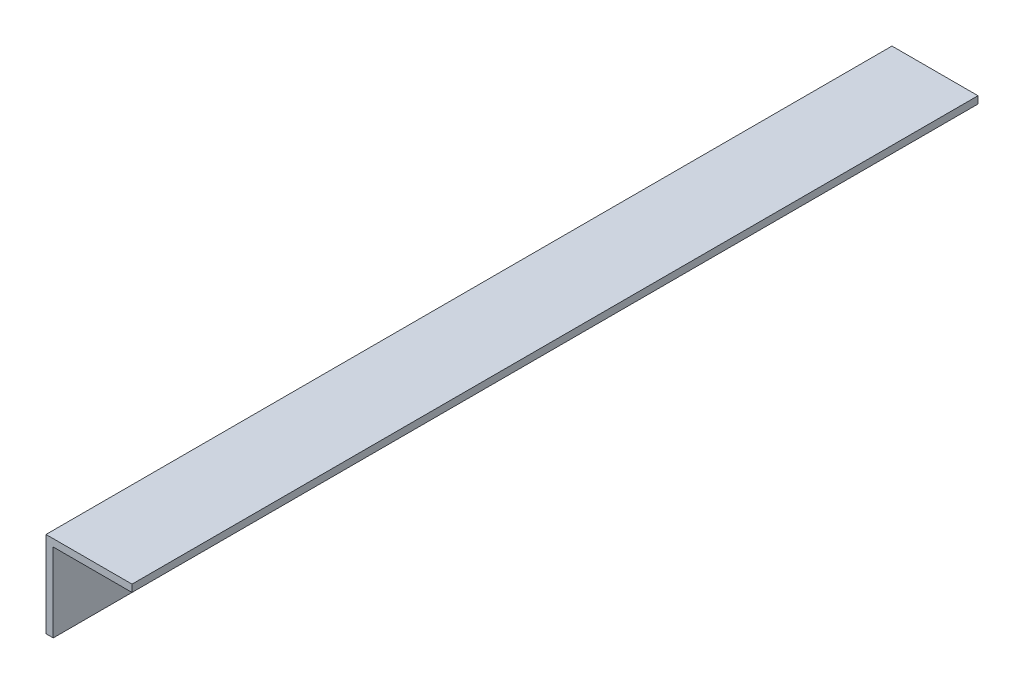
SolidWorks part; units mm, degrees
material "6061-T6 (SS)"
ref_plane "Front Plane" through (0, 0, 0) normal (0, 0, 1) x (1, 0, 0)
ref_plane "Top Plane" through (0, 0, 0) normal (0, 1, 0) x (1, 0, 0)
ref_plane "Right Plane" through (0, 0, 0) normal (1, 0, 0) x (0, 0, -1)
sketch "Sketch1" plane through (0, 0, 0) normal (0, 0, 1) x (1, 0, 0)
  line L0 (0, 0) -> (0, 19.05)
  line L1 (0, 19.05) -> (19.05, 19.05)
  line L2 (19.05, 19.05) -> (19.05, 17.4498)
  line L3 (19.05, 17.4498) -> (1.6002, 17.4498)
  line L4 (1.6002, 17.4498) -> (1.6002, 0)
  line L5 (1.6002, 0) -> (0, 0)
  dimension "D1" = 1.6002
  dimension "D2" = 19.05
extrude "Boss-Extrude1" add sketch "Sketch1" along normal blind 187.325
